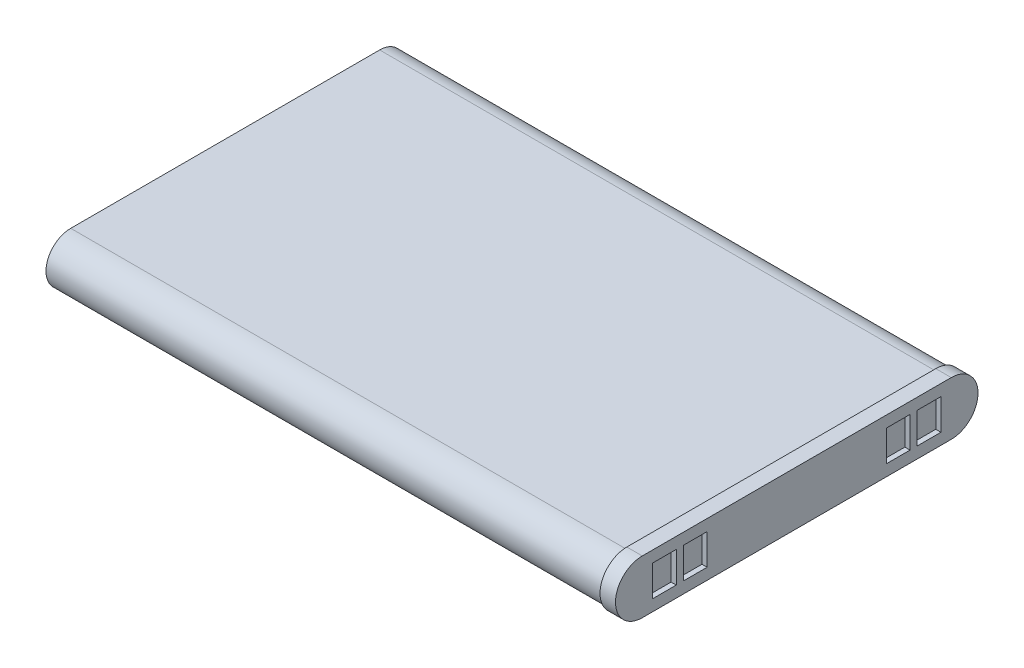
SolidWorks part; units mm, degrees
ref_plane "Front Plane" through (0, 0, 0) normal (0, 0, 1) x (1, 0, 0)
ref_plane "Top Plane" through (0, 0, 0) normal (0, 1, 0) x (1, 0, 0)
ref_plane "Right Plane" through (0, 0, 0) normal (1, 0, 0) x (0, 0, -1)
sketch "Sketch1" plane through (0, 0, 0) normal (1, 0, 0) x (0, 0, -1)
  line L0 (-15, 0) -> (15, 0) construction
  line L1 (-15, 2.4) -> (15, 2.4)
  line L2 (-15, -2.4) -> (15, -2.4)
  arc A0 (-15, 2.4) -> (-15, -2.4) centre (-15, 0) ccw
  arc A1 (15, -2.4) -> (15, 2.4) centre (15, 0) ccw
  point P2 (0, 0)
  dimension "D1" = 30
  dimension "D2" = 4.8
extrude "Boss-Extrude1" add sketch "Sketch1" along normal blind 54
sketch "Sketch2" plane through (54, 0, 0) normal (1, 0, 0) x (0, 0, -1)
  line L4 (-15, -2.6) -> (15, -2.6)
  line L5 (15, 2.6) -> (-15, 2.6)
  line L6 (-15, -2.6) -> (15, -2.6)
  line L7 (15, 2.6) -> (-15, 2.6)
  arc A4 (-15, 2.6) -> (-15, -2.6) centre (-15, 0) ccw
  arc A5 (15, -2.6) -> (15, 2.6) centre (15, 0) ccw
  arc A6 (-15, 2.6) -> (-15, -2.6) centre (-15, 0) ccw
  arc A7 (15, -2.6) -> (15, 2.6) centre (15, 0) ccw
  dimension "D1" = 0.2
extrude "Boss-Extrude2" add sketch "Sketch2" along normal blind 1.5
sketch "Sketch3" plane through (55.5, 0, 0) normal (1, 0, 0) x (0, 0, -1)
  line L0 (-17.6, 0) -> (17.6, 0) construction
  line L1 (-14, 1.5) -> (-11.7, 1.5)
  line L2 (-14, 1.5) -> (-14, -1.5)
  line L3 (-14, -1.5) -> (-11.7, -1.5)
  line L4 (-11.7, 1.5) -> (-11.7, -1.5)
  line L5 (-11, 1.5) -> (-8.7, 1.5)
  line L6 (-11, 1.5) -> (-11, -1.5)
  line L7 (-11, -1.5) -> (-8.7, -1.5)
  line L8 (-8.7, 1.5) -> (-8.7, -1.5)
  line L9 (0, 2.6) -> (0, -2.6) construction
  line L10 (15, 2.6) -> (-15, 2.6) construction
  line L11 (-15, -2.6) -> (15, -2.6) construction
  line L12 (8.7, 1.5) -> (8.7, -1.5)
  line L13 (11, -1.5) -> (8.7, -1.5)
  line L14 (11, 1.5) -> (11, -1.5)
  line L15 (11, 1.5) -> (8.7, 1.5)
  line L16 (11.7, 1.5) -> (11.7, -1.5)
  line L17 (14, -1.5) -> (11.7, -1.5)
  line L18 (14, 1.5) -> (14, -1.5)
  line L19 (14, 1.5) -> (11.7, 1.5)
  arc A0 (-15, 2.6) -> (-15, -2.6) centre (-15, 0) ccw construction
  arc A1 (15, -2.6) -> (15, 2.6) centre (15, 0) ccw construction
  point P11 (-17.6, 0)
  point P12 (-14, 0)
  dimension "D1" = 3
  dimension "D2" = 3.6
  dimension "D3" = 0.7
  dimension "D4" = 2.3
extrude "Cut-Extrude1" cut sketch "Sketch3" against normal blind 0.5
